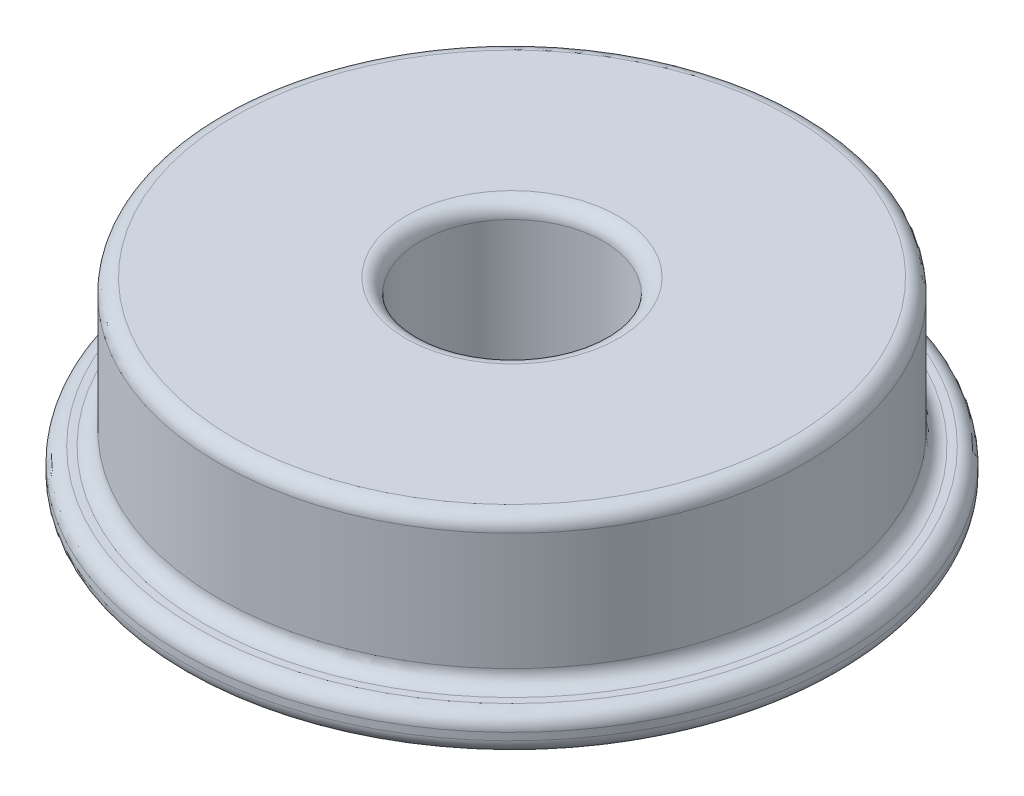
SolidWorks part; units mm, degrees
ref_plane "Front Plane" through (0, 0, 0) normal (0, 0, 1) x (1, 0, 0)
ref_plane "Top Plane" through (0, 0, 0) normal (0, 1, 0) x (1, 0, 0)
ref_plane "Right Plane" through (0, 0, 0) normal (1, 0, 0) x (0, 0, -1)
sketch "Sketch1" plane through (0, 0, 0) normal (0, 1, 0) x (1, 0, 0)
  circle A0 centre (0, 0) radius 9
  dimension "D1" = 18
extrude "Boss-Extrude1" add sketch "Sketch1" along normal blind 1
sketch "Sketch2" plane through (0, 1, 0) normal (0, 1, 0) x (1, 0, 0)
  circle A0 centre (0, 0) radius 8
  dimension "D1" = 16
extrude "Boss-Extrude2" add sketch "Sketch2" along normal blind 4
sketch "Sketch3" plane through (0, 5, 0) normal (0, 1, 0) x (1, 0, 0)
  circle A0 centre (0, 0) radius 2.5
  dimension "D1" = 5
extrude "Cut-Extrude1" cut sketch "Sketch3" against normal through all
fillet "Fillet1" radius 0.4 6 edges at (0, 5, 8) (0, 1, 8) (0, 1, 9) (0, 0, 9) (0, 0, 2.5) (0, 5, 2.5)
